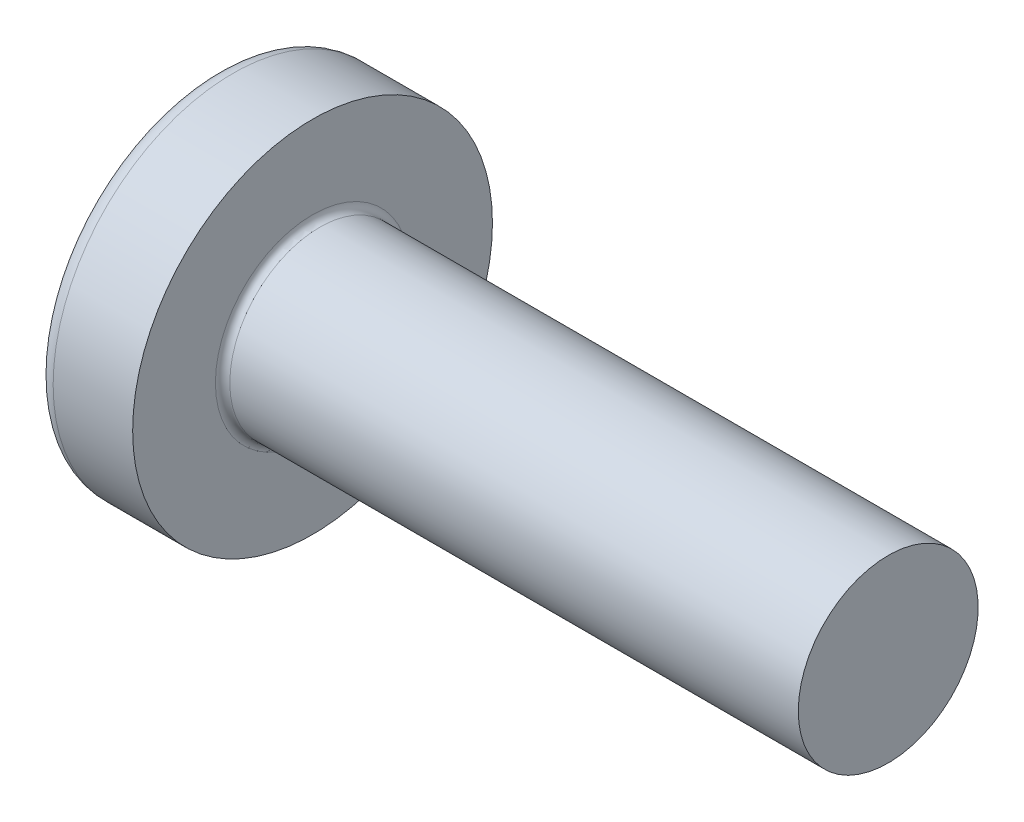
SolidWorks part; units mm, degrees
ref_plane "Plane1" through (0, 0, 0) normal (0, 0, 1) x (1, 0, 0)
ref_plane "Plane2" through (0, 0, 0) normal (0, 1, 0) x (1, 0, 0)
ref_plane "Plane3" through (0, 0, 0) normal (1, 0, 0) x (0, 0, -1)
sketch "BodySke" plane through (0, 0, 0) normal (0, 0, 1) x (1, 0, 0)
  line L0 (2.1, 1.25) -> (2.1, 2.5)
  line L1 (2.325, 6.35) -> (2.325, -3.175) construction
  line L2 (-25.4, 0) -> (127, 0) construction
  line L3 (10.1, 0) -> (0, 0)
  line L4 (2.1, 1.25) -> (10.1, 1.25)
  line L5 (10.1, 1.25) -> (10.1, 0)
  line L6 (0.995, 2.5) -> (2.1, 2.5)
  line L8 (2.1, 6.35) -> (2.1, -3.175) construction
  arc A0 (0.8032, 2.4043) -> (0, 0) centre (4, 0) ccw
  arc A2 (0.8032, 2.4043) -> (0.995, 2.5) centre (0.995, 2.26) cw
  dimension "Head_crown_rad" = 4
  dimension "Head_fillet_rad" = 0.24
  dimension "Length" = 8
  dimension "Head_ht" = 2.1
  dimension "Head_dia" = 5
  dimension "Advance" = 0.45
  dimension "Thread_nom" = 8
  dimension "Diameter" = 2.5
revolve "Base-Revolve" add sketch "BodySke"
cosmetic thread "ThreadCosmetic" [suppressed]
fillet "Fillet1" radius 0.1 1 edges at (2.1, 0, 1.25)
sketch "Sketch3" plane through (0, 0, 0) normal (1, 0, 0) x (0, 0, -1)
  line L0 (0.37, -1.3) -> (-0.37, -1.3)
  line L1 (0.37, -1.3) -> (0.37, 1.3)
  line L2 (-0.37, 1.3) -> (0.37, 1.3)
  line L3 (-0.37, 1.3) -> (-0.37, -1.3)
  dimension "Cross_dia" = 2.6
  dimension "D1" = 1.3
  dimension "Cross_width" = 0.74
  dimension "D2" = 0.37
ref_plane "Plane4" through (1.5, 0, 0) normal (1, 0, 0) x (0, 0, -1)
sketch "Sketch4" plane through (1.5, 0, 0) normal (1, 0, 0) x (0, 0, -1)
  line L0 (0.37, -0.5521) -> (-0.37, -0.5521)
  line L1 (0.37, -0.5521) -> (0.37, 0.5521)
  line L2 (-0.37, 0.5521) -> (0.37, 0.5521)
  line L3 (-0.37, 0.5521) -> (-0.37, -0.5521)
  dimension "D1" = 0.74
  dimension "D2" = 1.1043
  dimension "D3" = 0.37
  dimension "D4" = 0.5521
loft "Recess" cut profiles "Sketch3", "Sketch4"
pattern_circular "RecPat" count 2 every 90 about axis through (0, 0, 0) along (1, 0, 0) of "Recess"
sketch "RecCorSke" plane through (0, 0, 0) normal (0, 0, 1) x (1, 0, 0)
  line L0 (-3.175, 0) -> (15.875, 0) construction
  line L1 (-25.4, 0) -> (127, 0) construction
  line L2 (0, 0) -> (0, 0.6609)
  line L3 (0, 0.6609) -> (1.5, 0.556)
  line L4 (1.5, 0.556) -> (1.6807, 0)
  line L5 (1.6807, 0) -> (0, 0)
  dimension "Diameter" = 1.112
  dimension "Depth" = 1.5
  dimension "Draft_angle" = 4
  dimension "Bottom_angle" = 18
revolve "RecessCore" cut sketch "RecCorSke" angle 360 about L0
sketch "ThdSchSke" plane through (0, 0, 0) normal (0, 0, 1) x (1, 0, 0)
  line L0 (3, -0.9965) -> (2.8225, -1.25)
  line L1 (3, -0.9965) -> (3.1775, -1.25)
  line L2 (3.1775, -1.25) -> (3.1775, -1.5625)
  line L3 (-3.175, 0) -> (5.1513, 0) construction
  line L5 (3.1775, -1.5625) -> (2.8225, -1.5625)
  line L6 (2.8225, -1.5625) -> (2.8225, -1.25)
  dimension "Diameter" = 2.5
  dimension "SideAngle" = 55
  dimension "VeeAngle" = 70
  dimension "Thread_minor" = 1.993
  dimension "Overcut" = 3.125
  dimension "Start" = 3
revolve "ThreadSchematic" [suppressed] cut sketch "ThdSchSke" angle 360 about L3
pattern_linear "ThdSchPat" [suppressed]
equation "\"D1@Sketch3\" = \"Cross_dia@Sketch3\" / 2"
equation "\"D2@Sketch3\" = \"Cross_width@Sketch3\" / 2"
equation "\"Depth@RecCorSke\" = \"Cross_depth@Plane4\""
equation "\"D1@Sketch4\" = \"Cross_width@Sketch3\""
equation "\"D2@Sketch4\" = \"Cross_dia@Sketch3\" - 2.0 * \"Cross_depth@Plane4\" * tan(26.5  * 0.017453292)"
equation "\"D3@Sketch4\" = \"D1@Sketch4\" / 2"
equation "\"D4@Sketch4\" = \"D2@Sketch4\" / 2"
equation "\"Thread_length@ThreadCosmetic\" = ((sgn( (\"Length@BodySke\" - \"Advance@BodySke\" * 2.0 ) - \"Thread_nom@BodySke\" )-1)*( (\"Length@BodySke\" - \"Advance@BodySke\" * 2.0 ) - \"Thread_nom@BodySke\" ))/-2+ \"Thread_nom@BodySke\""
equation "\"Thread_minor@ThdSchSke\" = \"Thread_minor@ThreadCosmetic\""
equation "\"Diameter@ThdSchSke\" = \"Diameter@BodySke\""
equation "\"Overcut@ThdSchSke\" = \"Diameter@BodySke\" * 1.25"
equation "\"Start@ThdSchSke\" = \"Head_ht@BodySke\" + \"Length@BodySke\" - \"Thread_length@ThreadCosmetic\"  '---Non-countersunk---"
equation "\"Num_threads@ThdSchPat\" = int( \"Thread_length@ThreadCosmetic\" / \"Advance@BodySke\" + 0.999 )  + 1"
equation "\"Advance@ThdSchPat\" = \"Thread_length@ThreadCosmetic\" /  (\"Num_threads@ThdSchPat\" - 1) 'relax it"
